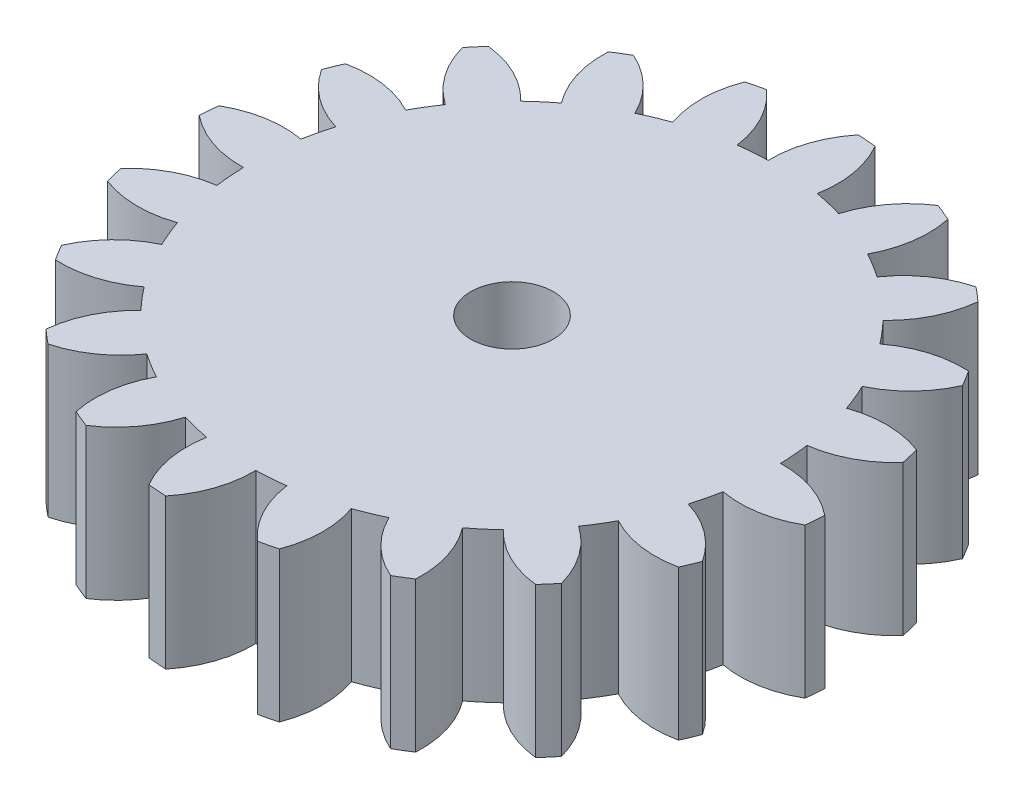
SolidWorks part; units mm, degrees
ref_plane "前视基准面" through (0, 0, 0) normal (0, 0, 1) x (1, 0, 0)
ref_plane "上视基准面" through (0, 0, 0) normal (0, 1, 0) x (1, 0, 0)
ref_plane "右视基准面" through (0, 0, 0) normal (1, 0, 0) x (0, 0, -1)
sketch "草图1" plane through (0, 0, 0) normal (0, 1, 0) x (1, 0, 0)
  line L0 (0, 0) -> (0, 22) construction
  line L1 (0, 0) -> (10.9643, 30.1242) construction
  line L2 (0, 0) -> (2.8303, 35.9623) construction
  line L3 (0, 20) -> (6.4279, 17.6604) construction
  circle A0 centre (0, 0) radius 22 construction
  circle A1 centre (0, 0) radius 17.5 construction
  circle A2 centre (0, 0) radius 20 construction
  circle A3 centre (6.4279, 17.6604) radius 6.8404 construction
  arc A4 (1.1171, 21.9716) -> (-0.4105, 17.4952) centre (6.4279, 17.6604) ccw
  arc A5 (2.3338, 21.8759) -> (3.1423, 17.2156) centre (-3.586, 18.4486) cw
  arc A6 (1.1171, 21.9716) -> (2.3338, 21.8759) centre (0, 0) cw
  arc A7 (7.852, 20.5511) -> (5.0159, 16.7658) centre (11.5707, 14.8098) ccw
  arc A8 (7.852, 20.5511) -> (8.9796, 20.084) centre (0, 0) cw
  arc A9 (8.9796, 20.084) -> (8.3084, 15.4019) centre (2.2904, 18.6538) cw
  arc A10 (13.8183, 17.1188) -> (9.9513, 14.3952) centre (15.5808, 10.5094) ccw
  arc A11 (13.8183, 17.1188) -> (14.7464, 16.3262) centre (0, 0) cw
  arc A12 (14.7464, 16.3262) -> (12.6613, 12.0807) centre (7.9426, 17.033) cw
  arc A13 (18.432, 12.0109) -> (13.9126, 10.6155) centre (18.0658, 5.1803) ccw
  arc A14 (18.432, 12.0109) -> (19.0697, 10.9702) centre (0, 0) cw
  arc A15 (19.0697, 10.9702) -> (15.7747, 7.5769) centre (12.8174, 13.745) cw
  arc A16 (21.2414, 5.7272) -> (16.512, 5.7967) centre (18.7824, -0.6559) ccw
  arc A17 (21.2414, 5.7272) -> (21.5264, 4.5404) centre (0, 0) cw
  arc A18 (21.5264, 4.5404) -> (17.344, 2.3314) centre (16.4375, 9.1114) cw
  arc A19 (21.9716, -1.1171) -> (17.4952, 0.4105) centre (17.6604, -6.4279) ccw
  arc A20 (21.9716, -1.1171) -> (21.8759, -2.3338) centre (0, 0) cw
  arc A21 (21.8759, -2.3338) -> (17.2156, -3.1423) centre (18.4486, 3.586) cw
  arc A22 (20.5511, -7.852) -> (16.7658, -5.0159) centre (14.8098, -11.5707) ccw
  arc A23 (20.5511, -7.852) -> (20.084, -8.9796) centre (0, 0) cw
  arc A24 (20.084, -8.9796) -> (15.4019, -8.3084) centre (18.6538, -2.2904) cw
  arc A25 (17.1188, -13.8183) -> (14.3952, -9.9513) centre (10.5094, -15.5808) ccw
  arc A26 (17.1188, -13.8183) -> (16.3262, -14.7464) centre (0, 0) cw
  arc A27 (16.3262, -14.7464) -> (12.0807, -12.6613) centre (17.033, -7.9426) cw
  arc A28 (12.0109, -18.432) -> (10.6155, -13.9126) centre (5.1803, -18.0658) ccw
  arc A29 (12.0109, -18.432) -> (10.9702, -19.0697) centre (0, 0) cw
  arc A30 (10.9702, -19.0697) -> (7.5769, -15.7747) centre (13.745, -12.8174) cw
  arc A31 (5.7272, -21.2414) -> (5.7967, -16.512) centre (-0.6559, -18.7824) ccw
  arc A32 (5.7272, -21.2414) -> (4.5404, -21.5264) centre (0, 0) cw
  arc A33 (4.5404, -21.5264) -> (2.3314, -17.344) centre (9.1114, -16.4375) cw
  arc A34 (-1.1171, -21.9716) -> (0.4105, -17.4952) centre (-6.4279, -17.6604) ccw
  arc A35 (-1.1171, -21.9716) -> (-2.3338, -21.8759) centre (0, 0) cw
  arc A36 (-2.3338, -21.8759) -> (-3.1423, -17.2156) centre (3.586, -18.4486) cw
  arc A37 (-7.852, -20.5511) -> (-5.0159, -16.7658) centre (-11.5707, -14.8098) ccw
  arc A38 (-7.852, -20.5511) -> (-8.9796, -20.084) centre (0, 0) cw
  arc A39 (-8.9796, -20.084) -> (-8.3084, -15.4019) centre (-2.2904, -18.6538) cw
  arc A40 (-13.8183, -17.1188) -> (-9.9513, -14.3952) centre (-15.5808, -10.5094) ccw
  arc A41 (-13.8183, -17.1188) -> (-14.7464, -16.3262) centre (0, 0) cw
  arc A42 (-14.7464, -16.3262) -> (-12.6613, -12.0807) centre (-7.9426, -17.033) cw
  arc A43 (-18.432, -12.0109) -> (-13.9126, -10.6155) centre (-18.0658, -5.1803) ccw
  arc A44 (-18.432, -12.0109) -> (-19.0697, -10.9702) centre (0, 0) cw
  arc A45 (-19.0697, -10.9702) -> (-15.7747, -7.5769) centre (-12.8174, -13.745) cw
  arc A46 (-21.2414, -5.7272) -> (-16.512, -5.7967) centre (-18.7824, 0.6559) ccw
  arc A47 (-21.2414, -5.7272) -> (-21.5264, -4.5404) centre (0, 0) cw
  arc A48 (-21.5264, -4.5404) -> (-17.344, -2.3314) centre (-16.4375, -9.1114) cw
  arc A49 (-21.9716, 1.1171) -> (-17.4952, -0.4105) centre (-17.6604, 6.4279) ccw
  arc A50 (-21.9716, 1.1171) -> (-21.8759, 2.3338) centre (0, 0) cw
  arc A51 (-21.8759, 2.3338) -> (-17.2156, 3.1423) centre (-18.4486, -3.586) cw
  arc A52 (-20.5511, 7.852) -> (-16.7658, 5.0159) centre (-14.8098, 11.5707) ccw
  arc A53 (-20.5511, 7.852) -> (-20.084, 8.9796) centre (0, 0) cw
  arc A54 (-20.084, 8.9796) -> (-15.4019, 8.3084) centre (-18.6538, 2.2904) cw
  arc A55 (-17.1188, 13.8183) -> (-14.3952, 9.9513) centre (-10.5094, 15.5808) ccw
  arc A56 (-17.1188, 13.8183) -> (-16.3262, 14.7464) centre (0, 0) cw
  arc A57 (-16.3262, 14.7464) -> (-12.0807, 12.6613) centre (-17.033, 7.9426) cw
  arc A58 (-12.0109, 18.432) -> (-10.6155, 13.9126) centre (-5.1803, 18.0658) ccw
  arc A59 (-12.0109, 18.432) -> (-10.9702, 19.0697) centre (0, 0) cw
  arc A60 (-10.9702, 19.0697) -> (-7.5769, 15.7747) centre (-13.745, 12.8174) cw
  arc A61 (-5.7272, 21.2414) -> (-5.7967, 16.512) centre (0.6559, 18.7824) ccw
  arc A62 (-5.7272, 21.2414) -> (-4.5404, 21.5264) centre (0, 0) cw
  arc A63 (-4.5404, 21.5264) -> (-2.3314, 17.344) centre (-9.1114, 16.4375) cw
  arc A64 (-2.3314, 17.344) -> (-0.4105, 17.4952) centre (0, 0) cw
  arc A65 (3.1423, 17.2156) -> (5.0159, 16.7658) centre (0, 0) cw
  arc A66 (8.3084, 15.4019) -> (9.9513, 14.3952) centre (0, 0) cw
  arc A67 (12.6613, 12.0807) -> (13.9126, 10.6155) centre (0, 0) cw
  arc A68 (15.7747, 7.5769) -> (16.512, 5.7967) centre (0, 0) cw
  arc A69 (17.344, 2.3314) -> (17.4952, 0.4105) centre (0, 0) cw
  arc A70 (17.2156, -3.1423) -> (16.7658, -5.0159) centre (0, 0) cw
  arc A71 (15.4019, -8.3084) -> (14.3952, -9.9513) centre (0, 0) cw
  arc A72 (12.0807, -12.6613) -> (10.6155, -13.9126) centre (0, 0) cw
  arc A73 (7.5769, -15.7747) -> (5.7967, -16.512) centre (0, 0) cw
  arc A74 (2.3314, -17.344) -> (0.4105, -17.4952) centre (0, 0) cw
  arc A75 (-3.1423, -17.2156) -> (-5.0159, -16.7658) centre (0, 0) cw
  arc A76 (-8.3084, -15.4019) -> (-9.9513, -14.3952) centre (0, 0) cw
  arc A77 (-12.6613, -12.0807) -> (-13.9126, -10.6155) centre (0, 0) cw
  arc A78 (-15.7747, -7.5769) -> (-16.512, -5.7967) centre (0, 0) cw
  arc A79 (-17.344, -2.3314) -> (-17.4952, -0.4105) centre (0, 0) cw
  arc A80 (-17.2156, 3.1423) -> (-16.7658, 5.0159) centre (0, 0) cw
  arc A81 (-15.4019, 8.3084) -> (-14.3952, 9.9513) centre (0, 0) cw
  arc A82 (-12.0807, 12.6613) -> (-10.6155, 13.9126) centre (0, 0) cw
  arc A83 (-7.5769, 15.7747) -> (-5.7967, 16.512) centre (0, 0) cw
  point P134 (0, 0)
  point P174 (0, 0)
  dimension "D1" = 40
  dimension "D2" = 44
  dimension "D3" = 35
  dimension "D4" = 20
  dimension "D5" = 4.5
  dimension "D6" = 20
  dimension "D7" = 20
extrude "凸台-拉伸1" add sketch "草图1" along normal blind 10 contours A83 A60 A59 A58 A82 A57 A56 A55 A81 A54 A53 A52 A80 A51 A50 A49 A79 A48 A47 A46 A78 A45 A44 A43 A77 A42 A41 A40 A76 A39 A38 A37 A75 A36 A35 A34 A74 A33 A32 A31 A73 A30 A29 A28 A72 A27 A26 A25 A71 A24 A23
sketch "草图2" plane through (0, 10, 0) normal (0, 1, 0) x (1, 0, 0)
  circle A0 centre (0, 0) radius 2.7524
extrude "切除-拉伸1" cut sketch "草图2" against normal through all both and the other way through all
